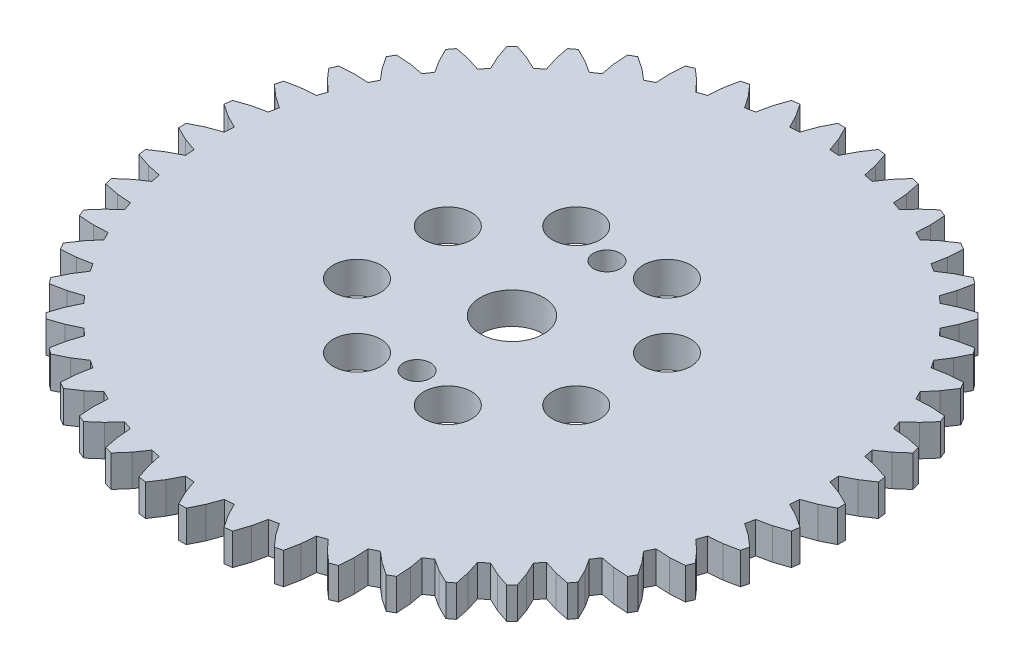
SolidWorks part; units mm, degrees
material "Acrylic (Medium-high impact)"
ref_plane "Front Plane" through (0, 0, 0) normal (0, 0, 1) x (1, 0, 0)
ref_plane "Top Plane" through (0, 0, 0) normal (0, 1, 0) x (1, 0, 0)
ref_plane "Right Plane" through (0, 0, 0) normal (1, 0, 0) x (0, 0, -1)
sketch "Sketch1" plane through (0, 0, 0) normal (0, 1, 0) x (1, 0, 0)
  line L0 (42.6708, 7.332) -> (44.3641, 6.7228)
  line L1 (44.3641, 6.7228) -> (46.0493, 5.8976)
  line L2 (46.0493, 5.8976) -> (46.0493, 4.9305)
  line L3 (46.0493, 4.9305) -> (44.3641, 4.1053)
  line L4 (44.3641, 4.1053) -> (42.6708, 3.4961)
  line L5 (42.6708, 3.4961) -> (42.5937, 2.3184)
  line L6 (42.5937, 2.3184) -> (44.1929, 1.4933)
  line L7 (44.1929, 1.4933) -> (45.7561, 0.4552)
  line L8 (45.7561, 0.4552) -> (45.6298, -0.5035)
  line L9 (45.6298, -0.5035) -> (43.8512, -1.1018)
  line L10 (43.8512, -1.1018) -> (42.093, -1.4848)
  line L11 (42.093, -1.4848) -> (41.8627, -2.6423)
  line L12 (41.8627, -2.6423) -> (43.3406, -3.669)
  line L13 (43.3406, -3.669) -> (44.7548, -4.9023)
  line L14 (44.7548, -4.9023) -> (44.5045, -5.8364)
  line L15 (44.5045, -5.8364) -> (42.663, -6.1973)
  line L16 (42.663, -6.1973) -> (40.8698, -6.3476)
  line L17 (40.8698, -6.3476) -> (40.4905, -7.4651)
  line L18 (40.4905, -7.4651) -> (41.8218, -8.676)
  line L19 (41.8218, -8.676) -> (43.0629, -10.0833)
  line L20 (43.0629, -10.0833) -> (42.6929, -10.9767)
  line L21 (42.6929, -10.9767) -> (40.82, -11.0943)
  line L22 (40.82, -11.0943) -> (39.0225, -11.0092)
  line L23 (39.0225, -11.0092) -> (38.5006, -12.0676)
  line L24 (38.5006, -12.0676) -> (39.6623, -13.4418)
  line L25 (39.6623, -13.4418) -> (40.7092, -14.9991)
  line L26 (40.7092, -14.9991) -> (40.2257, -15.8366)
  line L27 (40.2257, -15.8366) -> (38.3536, -15.7088)
  line L28 (38.3536, -15.7088) -> (36.5825, -15.3898)
  line L29 (36.5825, -15.3898) -> (35.9268, -16.371)
  line L30 (35.9268, -16.371) -> (36.8994, -17.8851)
  line L31 (36.8994, -17.8851) -> (37.734, -19.5657)
  line L32 (37.734, -19.5657) -> (37.1454, -20.3329)
  line L33 (37.1454, -20.3329) -> (35.3059, -19.9617)
  line L34 (35.3059, -19.9617) -> (33.5917, -19.4143)
  line L35 (33.5917, -19.4143) -> (32.8135, -20.3016)
  line L36 (32.8135, -20.3016) -> (33.58, -21.9296)
  line L37 (33.58, -21.9296) -> (34.1882, -23.7049)
  line L38 (34.1882, -23.7049) -> (33.5044, -24.3887)
  line L39 (33.5044, -24.3887) -> (31.7291, -23.7806)
  line L40 (31.7291, -23.7806) -> (30.1011, -23.014)
  line L41 (30.1011, -23.014) -> (29.2137, -23.7922)
  line L42 (29.2137, -23.7922) -> (29.7612, -25.5065)
  line L43 (29.7612, -25.5065) -> (30.1324, -27.3459)
  line L44 (30.1324, -27.3459) -> (29.3652, -27.9345)
  line L45 (29.3652, -27.9345) -> (27.6846, -27.0999)
  line L46 (27.6846, -27.0999) -> (26.1704, -26.1273)
  line L47 (26.1704, -26.1273) -> (25.1892, -26.783)
  line L48 (25.1892, -26.783) -> (25.5082, -28.5541)
  line L49 (25.5082, -28.5541) -> (25.6361, -30.4262)
  line L50 (25.6361, -30.4262) -> (24.7986, -30.9098)
  line L51 (24.7986, -30.9098) -> (23.2413, -29.8628)
  line L52 (23.2413, -29.8628) -> (21.8671, -28.7011)
  line L53 (21.8671, -28.7011) -> (20.8086, -29.223)
  line L54 (20.8086, -29.223) -> (20.8937, -31.0205)
  line L55 (20.8937, -31.0205) -> (20.7762, -32.8934)
  line L56 (20.7762, -32.8934) -> (19.8828, -33.2635)
  line L57 (19.8828, -33.2635) -> (18.4755, -32.0223)
  line L58 (18.4755, -32.0223) -> (17.2645, -30.691)
  line L59 (17.2645, -30.691) -> (16.147, -31.0704)
  line L60 (16.147, -31.0704) -> (15.9968, -32.8636)
  line L61 (15.9968, -32.8636) -> (15.6359, -34.7051)
  line L62 (15.6359, -34.7051) -> (14.7018, -34.9554)
  line L63 (14.7018, -34.9554) -> (13.4684, -33.5411)
  line L64 (13.4684, -33.5411) -> (12.4418, -32.0633)
  line L65 (12.4418, -32.0633) -> (11.2842, -32.2935)
  line L66 (11.2842, -32.2935) -> (10.9012, -34.0518)
  line L67 (10.9012, -34.0518) -> (10.303, -35.8303)
  line L68 (10.303, -35.8303) -> (9.3443, -35.9566)
  line L69 (9.3443, -35.9566) -> (8.3061, -34.3934)
  line L70 (8.3061, -34.3934) -> (7.4811, -32.7942)
  line L71 (7.4811, -32.7942) -> (6.3034, -32.8713)
  line L72 (6.3034, -32.8713) -> (5.6941, -34.5646)
  line L73 (5.6941, -34.5646) -> (4.869, -36.2498)
  line L74 (4.869, -36.2498) -> (3.9019, -36.2498)
  line L75 (3.9019, -36.2498) -> (3.0767, -34.5646)
  line L76 (3.0767, -34.5646) -> (2.4675, -32.8713)
  line L77 (2.4675, -32.8713) -> (1.2898, -32.7942)
  line L78 (1.2898, -32.7942) -> (0.4647, -34.3934)
  line L79 (0.4647, -34.3934) -> (-0.5735, -35.9566)
  line L80 (-0.5735, -35.9566) -> (-1.5322, -35.8303)
  line L81 (-1.5322, -35.8303) -> (-2.1304, -34.0518)
  line L82 (-2.1304, -34.0518) -> (-2.5134, -32.2935)
  line L83 (-2.5134, -32.2935) -> (-3.671, -32.0633)
  line L84 (-3.671, -32.0633) -> (-4.6976, -33.5411)
  line L85 (-4.6976, -33.5411) -> (-5.9309, -34.9554)
  line L86 (-5.9309, -34.9554) -> (-6.865, -34.7051)
  line L87 (-6.865, -34.7051) -> (-7.2259, -32.8636)
  line L88 (-7.2259, -32.8636) -> (-7.3762, -31.0704)
  line L89 (-7.3762, -31.0704) -> (-8.4937, -30.691)
  line L90 (-8.4937, -30.691) -> (-9.7047, -32.0223)
  line L91 (-9.7047, -32.0223) -> (-11.112, -33.2635)
  line L92 (-11.112, -33.2635) -> (-12.0054, -32.8934)
  line L93 (-12.0054, -32.8934) -> (-12.1229, -31.0205)
  line L94 (-12.1229, -31.0205) -> (-12.0378, -29.223)
  line L95 (-12.0378, -29.223) -> (-13.0963, -28.7011)
  line L96 (-13.0963, -28.7011) -> (-14.4705, -29.8628)
  line L97 (-14.4705, -29.8628) -> (-16.0278, -30.9098)
  line L98 (-16.0278, -30.9098) -> (-16.8653, -30.4262)
  line L99 (-16.8653, -30.4262) -> (-16.7374, -28.5541)
  line L100 (-16.7374, -28.5541) -> (-16.4184, -26.783)
  line L101 (-16.4184, -26.783) -> (-17.3996, -26.1273)
  line L102 (-17.3996, -26.1273) -> (-18.9137, -27.0999)
  line L103 (-18.9137, -27.0999) -> (-20.5944, -27.9345)
  line L104 (-20.5944, -27.9345) -> (-21.3616, -27.3459)
  line L105 (-21.3616, -27.3459) -> (-20.9903, -25.5065)
  line L106 (-20.9903, -25.5065) -> (-20.4429, -23.7922)
  line L107 (-20.4429, -23.7922) -> (-21.3303, -23.014)
  line L108 (-21.3303, -23.014) -> (-22.9583, -23.7806)
  line L109 (-22.9583, -23.7806) -> (-24.7335, -24.3887)
  line L110 (-24.7335, -24.3887) -> (-25.4174, -23.7049)
  line L111 (-25.4174, -23.7049) -> (-24.8092, -21.9296)
  line L112 (-24.8092, -21.9296) -> (-24.0427, -20.3016)
  line L113 (-24.0427, -20.3016) -> (-24.8209, -19.4143)
  line L114 (-24.8209, -19.4143) -> (-26.5351, -19.9617)
  line L115 (-26.5351, -19.9617) -> (-28.3745, -20.3329)
  line L116 (-28.3745, -20.3329) -> (-28.9632, -19.5657)
  line L117 (-28.9632, -19.5657) -> (-28.1286, -17.8851)
  line L118 (-28.1286, -17.8851) -> (-27.156, -16.371)
  line L119 (-27.156, -16.371) -> (-27.8117, -15.3898)
  line L120 (-27.8117, -15.3898) -> (-29.5827, -15.7088)
  line L121 (-29.5827, -15.7088) -> (-31.4549, -15.8366)
  line L122 (-31.4549, -15.8366) -> (-31.9384, -14.9991)
  line L123 (-31.9384, -14.9991) -> (-30.8915, -13.4418)
  line L124 (-30.8915, -13.4418) -> (-29.7297, -12.0676)
  line L125 (-29.7297, -12.0676) -> (-30.2516, -11.0092)
  line L126 (-30.2516, -11.0092) -> (-32.0492, -11.0943)
  line L127 (-32.0492, -11.0943) -> (-33.9221, -10.9767)
  line L128 (-33.9221, -10.9767) -> (-34.2921, -10.0833)
  line L129 (-34.2921, -10.0833) -> (-33.0509, -8.676)
  line L130 (-33.0509, -8.676) -> (-31.7197, -7.4651)
  line L131 (-31.7197, -7.4651) -> (-32.099, -6.3476)
  line L132 (-32.099, -6.3476) -> (-33.8922, -6.1973)
  line L133 (-33.8922, -6.1973) -> (-35.7337, -5.8364)
  line L134 (-35.7337, -5.8364) -> (-35.984, -4.9023)
  line L135 (-35.984, -4.9023) -> (-34.5698, -3.669)
  line L136 (-34.5698, -3.669) -> (-33.0919, -2.6423)
  line L137 (-33.0919, -2.6423) -> (-33.3222, -1.4848)
  line L138 (-33.3222, -1.4848) -> (-35.0804, -1.1018)
  line L139 (-35.0804, -1.1018) -> (-36.8589, -0.5035)
  line L140 (-36.8589, -0.5035) -> (-36.9853, 0.4552)
  line L141 (-36.9853, 0.4552) -> (-35.4221, 1.4933)
  line L142 (-35.4221, 1.4933) -> (-33.8228, 2.3184)
  line L143 (-33.8228, 2.3184) -> (-33.8999, 3.4961)
  line L144 (-33.8999, 3.4961) -> (-35.5933, 4.1053)
  line L145 (-35.5933, 4.1053) -> (-37.2785, 4.9305)
  line L146 (-37.2785, 4.9305) -> (-37.2785, 5.8976)
  line L147 (-37.2785, 5.8976) -> (-35.5933, 6.7228)
  line L148 (-35.5933, 6.7228) -> (-33.8999, 7.332)
  line L149 (-33.8999, 7.332) -> (-33.8228, 8.5097)
  line L150 (-33.8228, 8.5097) -> (-35.4221, 9.3348)
  line L151 (-35.4221, 9.3348) -> (-36.9853, 10.3729)
  line L152 (-36.9853, 10.3729) -> (-36.8589, 11.3316)
  line L153 (-36.8589, 11.3316) -> (-35.0804, 11.9299)
  line L154 (-35.0804, 11.9299) -> (-33.3222, 12.3129)
  line L155 (-33.3222, 12.3129) -> (-33.0919, 13.4704)
  line L156 (-33.0919, 13.4704) -> (-34.5698, 14.4971)
  line L157 (-34.5698, 14.4971) -> (-35.984, 15.7304)
  line L158 (-35.984, 15.7304) -> (-35.7337, 16.6645)
  line L159 (-35.7337, 16.6645) -> (-33.8922, 17.0254)
  line L160 (-33.8922, 17.0254) -> (-32.099, 17.1757)
  line L161 (-32.099, 17.1757) -> (-31.7197, 18.2932)
  line L162 (-31.7197, 18.2932) -> (-33.0509, 19.5041)
  line L163 (-33.0509, 19.5041) -> (-34.2921, 20.9114)
  line L164 (-34.2921, 20.9114) -> (-33.9221, 21.8048)
  line L165 (-33.9221, 21.8048) -> (-32.0492, 21.9224)
  line L166 (-32.0492, 21.9224) -> (-30.2516, 21.8373)
  line L167 (-30.2516, 21.8373) -> (-29.7297, 22.8957)
  line L168 (-29.7297, 22.8957) -> (-30.8915, 24.2699)
  line L169 (-30.8915, 24.2699) -> (-31.9384, 25.8272)
  line L170 (-31.9384, 25.8272) -> (-31.4549, 26.6647)
  line L171 (-31.4549, 26.6647) -> (-29.5827, 26.5368)
  line L172 (-29.5827, 26.5368) -> (-27.8117, 26.2178)
  line L173 (-27.8117, 26.2178) -> (-27.156, 27.1991)
  line L174 (-27.156, 27.1991) -> (-28.1286, 28.7132)
  line L175 (-28.1286, 28.7132) -> (-28.9632, 30.3938)
  line L176 (-28.9632, 30.3938) -> (-28.3745, 31.161)
  line L177 (-28.3745, 31.161) -> (-26.5351, 30.7898)
  line L178 (-26.5351, 30.7898) -> (-24.8209, 30.2424)
  line L179 (-24.8209, 30.2424) -> (-24.0427, 31.1297)
  line L180 (-24.0427, 31.1297) -> (-24.8092, 32.7577)
  line L181 (-24.8092, 32.7577) -> (-25.4174, 34.533)
  line L182 (-25.4174, 34.533) -> (-24.7335, 35.2168)
  line L183 (-24.7335, 35.2168) -> (-22.9583, 34.6087)
  line L184 (-22.9583, 34.6087) -> (-21.3303, 33.8421)
  line L185 (-21.3303, 33.8421) -> (-20.4429, 34.6203)
  line L186 (-20.4429, 34.6203) -> (-20.9903, 36.3346)
  line L187 (-20.9903, 36.3346) -> (-21.3616, 38.174)
  line L188 (-21.3616, 38.174) -> (-20.5944, 38.7626)
  line L189 (-20.5944, 38.7626) -> (-18.9137, 37.928)
  line L190 (-18.9137, 37.928) -> (-17.3996, 36.9554)
  line L191 (-17.3996, 36.9554) -> (-16.4184, 37.6111)
  line L192 (-16.4184, 37.6111) -> (-16.7374, 39.3822)
  line L193 (-16.7374, 39.3822) -> (-16.8653, 41.2543)
  line L194 (-16.8653, 41.2543) -> (-16.0278, 41.7379)
  line L195 (-16.0278, 41.7379) -> (-14.4705, 40.6909)
  line L196 (-14.4705, 40.6909) -> (-13.0963, 39.5292)
  line L197 (-13.0963, 39.5292) -> (-12.0378, 40.0511)
  line L198 (-12.0378, 40.0511) -> (-12.1229, 41.8486)
  line L199 (-12.1229, 41.8486) -> (-12.0054, 43.7215)
  line L200 (-12.0054, 43.7215) -> (-11.112, 44.0916)
  line L201 (-11.112, 44.0916) -> (-9.7047, 42.8504)
  line L202 (-9.7047, 42.8504) -> (-8.4937, 41.5191)
  line L203 (-8.4937, 41.5191) -> (-7.3762, 41.8985)
  line L204 (-7.3762, 41.8985) -> (-7.2259, 43.6917)
  line L205 (-7.2259, 43.6917) -> (-6.865, 45.5332)
  line L206 (-6.865, 45.5332) -> (-5.9309, 45.7835)
  line L207 (-5.9309, 45.7835) -> (-4.6976, 44.3692)
  line L208 (-4.6976, 44.3692) -> (-3.671, 42.8914)
  line L209 (-3.671, 42.8914) -> (-2.5134, 43.1216)
  line L210 (-2.5134, 43.1216) -> (-2.1304, 44.8799)
  line L211 (-2.1304, 44.8799) -> (-1.5322, 46.6584)
  line L212 (-1.5322, 46.6584) -> (-0.5735, 46.7847)
  line L213 (-0.5735, 46.7847) -> (0.4647, 45.2215)
  line L214 (0.4647, 45.2215) -> (1.2898, 43.6223)
  line L215 (1.2898, 43.6223) -> (2.4675, 43.6994)
  line L216 (2.4675, 43.6994) -> (3.0767, 45.3927)
  line L217 (3.0767, 45.3927) -> (3.9019, 47.0779)
  line L218 (3.9019, 47.0779) -> (4.869, 47.0779)
  line L219 (4.869, 47.0779) -> (5.6941, 45.3927)
  line L220 (5.6941, 45.3927) -> (6.3034, 43.6994)
  line L221 (6.3034, 43.6994) -> (7.4811, 43.6223)
  line L222 (7.4811, 43.6223) -> (8.3061, 45.2215)
  line L223 (8.3061, 45.2215) -> (9.3443, 46.7847)
  line L224 (9.3443, 46.7847) -> (10.303, 46.6584)
  line L225 (10.303, 46.6584) -> (10.9012, 44.8799)
  line L226 (10.9012, 44.8799) -> (11.2842, 43.1216)
  line L227 (11.2842, 43.1216) -> (12.4418, 42.8914)
  line L228 (12.4418, 42.8914) -> (13.4684, 44.3692)
  line L229 (13.4684, 44.3692) -> (14.7018, 45.7835)
  line L230 (14.7018, 45.7835) -> (15.6359, 45.5332)
  line L231 (15.6359, 45.5332) -> (15.9968, 43.6917)
  line L232 (15.9968, 43.6917) -> (16.147, 41.8985)
  line L233 (16.147, 41.8985) -> (17.2645, 41.5191)
  line L234 (17.2645, 41.5191) -> (18.4755, 42.8504)
  line L235 (18.4755, 42.8504) -> (19.8828, 44.0916)
  line L236 (19.8828, 44.0916) -> (20.7762, 43.7215)
  line L237 (20.7762, 43.7215) -> (20.8937, 41.8486)
  line L238 (20.8937, 41.8486) -> (20.8086, 40.0511)
  line L239 (20.8086, 40.0511) -> (21.8671, 39.5292)
  line L240 (21.8671, 39.5292) -> (23.2413, 40.6909)
  line L241 (23.2413, 40.6909) -> (24.7986, 41.7379)
  line L242 (24.7986, 41.7379) -> (25.6361, 41.2543)
  line L243 (25.6361, 41.2543) -> (25.5082, 39.3822)
  line L244 (25.5082, 39.3822) -> (25.1892, 37.6111)
  line L245 (25.1892, 37.6111) -> (26.1704, 36.9554)
  line L246 (26.1704, 36.9554) -> (27.6846, 37.928)
  line L247 (27.6846, 37.928) -> (29.3652, 38.7626)
  line L248 (29.3652, 38.7626) -> (30.1324, 38.174)
  line L249 (30.1324, 38.174) -> (29.7612, 36.3346)
  line L250 (29.7612, 36.3346) -> (29.2137, 34.6203)
  line L251 (29.2137, 34.6203) -> (30.1011, 33.8421)
  line L252 (30.1011, 33.8421) -> (31.7291, 34.6087)
  line L253 (31.7291, 34.6087) -> (33.5044, 35.2168)
  line L254 (33.5044, 35.2168) -> (34.1882, 34.533)
  line L255 (34.1882, 34.533) -> (33.58, 32.7577)
  line L256 (33.58, 32.7577) -> (32.8135, 31.1297)
  line L257 (32.8135, 31.1297) -> (33.5917, 30.2424)
  line L258 (33.5917, 30.2424) -> (35.3059, 30.7898)
  line L259 (35.3059, 30.7898) -> (37.1454, 31.161)
  line L260 (37.1454, 31.161) -> (37.734, 30.3938)
  line L261 (37.734, 30.3938) -> (36.8994, 28.7132)
  line L262 (36.8994, 28.7132) -> (35.9268, 27.1991)
  line L263 (35.9268, 27.1991) -> (36.5825, 26.2178)
  line L264 (36.5825, 26.2178) -> (38.3536, 26.5368)
  line L265 (38.3536, 26.5368) -> (40.2257, 26.6647)
  line L266 (40.2257, 26.6647) -> (40.7092, 25.8272)
  line L267 (40.7092, 25.8272) -> (39.6623, 24.2699)
  line L268 (39.6623, 24.2699) -> (38.5006, 22.8957)
  line L269 (38.5006, 22.8957) -> (39.0225, 21.8373)
  line L270 (39.0225, 21.8373) -> (40.82, 21.9224)
  line L271 (40.82, 21.9224) -> (42.6929, 21.8048)
  line L272 (42.6929, 21.8048) -> (43.0629, 20.9114)
  line L273 (43.0629, 20.9114) -> (41.8218, 19.5041)
  line L274 (41.8218, 19.5041) -> (40.4905, 18.2932)
  line L275 (40.4905, 18.2932) -> (40.8698, 17.1757)
  line L276 (40.8698, 17.1757) -> (42.663, 17.0254)
  line L277 (42.663, 17.0254) -> (44.5045, 16.6645)
  line L278 (44.5045, 16.6645) -> (44.7548, 15.7304)
  line L279 (44.7548, 15.7304) -> (43.3406, 14.4971)
  line L280 (43.3406, 14.4971) -> (41.8627, 13.4704)
  line L281 (41.8627, 13.4704) -> (42.093, 12.3129)
  line L282 (42.093, 12.3129) -> (43.8512, 11.9299)
  line L283 (43.8512, 11.9299) -> (45.6298, 11.3316)
  line L284 (45.6298, 11.3316) -> (45.7561, 10.3729)
  line L285 (45.7561, 10.3729) -> (44.1929, 9.3348)
  line L286 (44.1929, 9.3348) -> (42.5937, 8.5097)
  line L287 (42.5937, 8.5097) -> (42.6708, 7.332)
  line L288 (4.3854, 47.0779) -> (4.3854, -36.2498) construction
  line L289 (-37.2785, 5.414) -> (46.0493, 5.414) construction
  point P292 (4.3854, 5.414)
sketch "Sketch3" plane through (0, 0, 0) normal (0, 1, 0) x (1, 0, 0)
  line L0 (-37.2785, 5.414) -> (46.0493, 5.414) construction
  circle A0 centre (4.3854, 5.414) radius 4
  dimension "D1" = 8
sketch "Sketch4" plane through (0, 0, 0) normal (0, 1, 0) x (1, 0, 0)
  line L0 (-12.0218, 5.414) -> (22.4064, 5.414) construction
  line L1 (-37.2785, 5.414) -> (46.0493, 5.414) construction
  line L2 (4.3854, 47.0779) -> (4.3854, -36.2498) construction
  circle A0 centre (4.3854, 17.414) radius 1.7
  circle A1 centre (4.3854, -6.586) radius 1.7
  dimension "D1" = 3.4
  dimension "D2" = 12
extrude "Boss-Extrude2" add sketch "Sketch1" along normal blind 4
extrude "Cut-Extrude1" cut sketch "Sketch3" along normal up to next
extrude "Cut-Extrude2" cut sketch "Sketch4" along normal up to next
sketch "Sketch5" plane through (0, 0, 0) normal (0, 1, 0) x (1, 0, 0)
  line L0 (4.3854, 5.414) -> (4.3854, 47.0779) construction
  line L1 (4.869, 47.0779) -> (3.9019, 47.0779) construction
  line L2 (4.3854, 5.414) -> (22.1331, 48.2608) construction
  circle A0 centre (10.1257, 19.2722) radius 3
  point P0 (4.3854, 5.414)
  dimension "D2" = 6
  dimension "D1" = 22.5
  dimension "D3" = 15
extrude "Cut-Extrude3" cut sketch "Sketch5" along normal up to next (4 mm away)
pattern_circular "CirPattern1" count 8 over 360 about axis through (4.3854, 0, -5.414) along (0, 1, 0) of "Cut-Extrude3"
